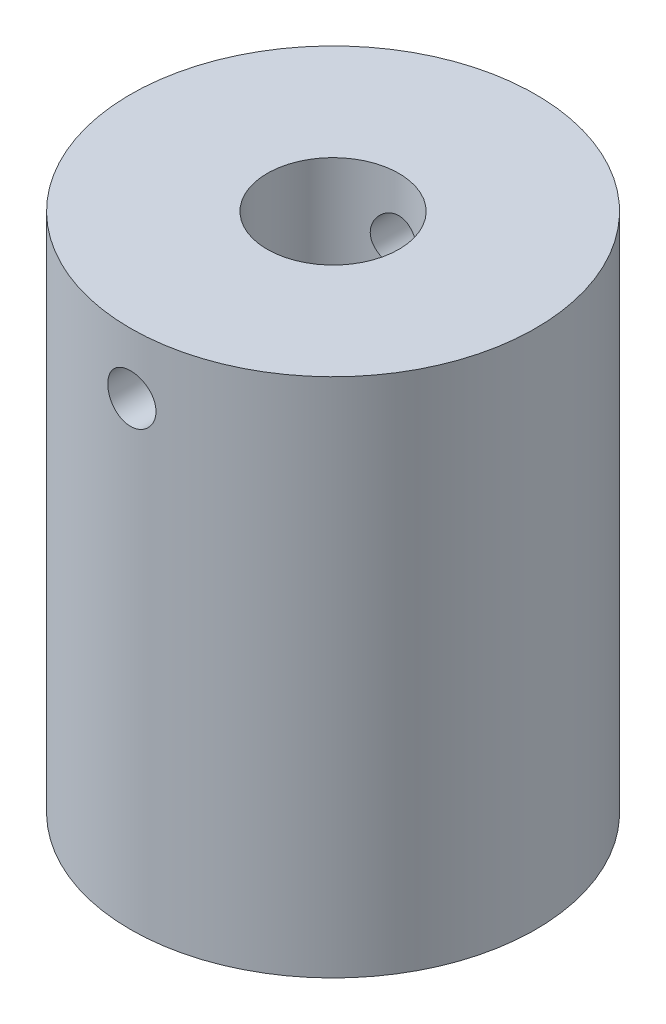
SolidWorks part; units mm, degrees
ref_plane "Front Plane" through (0, 0, 0) normal (0, 0, 1) x (1, 0, 0)
ref_plane "Top Plane" through (0, 0, 0) normal (0, 1, 0) x (1, 0, 0)
ref_plane "Right Plane" through (0, 0, 0) normal (1, 0, 0) x (0, 0, -1)
sketch "Sketch1" plane through (0, 0, 0) normal (0, 1, 0) x (1, 0, 0)
  circle A0 centre (0, 0) radius 7.2571
  dimension "D1" = 14.5143
extrude "Boss-Extrude1" add sketch "Sketch1" along normal blind 18.6509
sketch "Sketch2" plane through (0, 18.6509, 0) normal (0, 1, 0) x (1, 0, 0)
  circle A2 centre (0, 0) radius 2.3586
  dimension "D1" = 4.7171
extrude "Cut-Extrude1" cut sketch "Sketch2" against normal blind 5.4429
sketch "Sketch3" plane through (0, 0, 0) normal (0, -1, 0) x (1, 0, 0)
  line L0 (-1.0089, 1.9812) -> (1.0089, 1.9812)
  arc A0 (-1.4694, 1.8333) -> (1.4694, 1.8333) centre (0, 0) ccw
  arc A1 (-1.0089, 1.9812) -> (-1.4694, 1.8333) centre (-1.2629, 1.9812) ccw
  arc A2 (1.0089, 1.9812) -> (1.4694, 1.8333) centre (1.2629, 1.9812) cw
  dimension "D1" = 4.699
  dimension "D3" = 0.254
  dimension "D2" = 1.9812
extrude "Cut-Extrude2" cut sketch "Sketch3" against normal blind 10.16
ref_plane "Plane1" through (0, 10.16, 0) normal (0, -1, 0) x (-1, 0, 0)
ref_plane "Plane2" through (0, 0, 7.2571) normal (0, 0, 1) x (1, 0, 0)
sketch "Sketch4" plane through (0, 0, 7.2571) normal (0, 0, 1) x (1, 0, 0)
  line L0 (7.2571, 18.6509) -> (-7.2571, 18.6509) construction
  circle A0 centre (0, 16.4737) radius 0.8636
  dimension "D2" = 1.7272
  dimension "D1" = 2.1771
extrude "Cut-Extrude3" cut sketch "Sketch4" against normal through all
scale "Scale1" scale about centroid uniform scaling yes scale factor 1.75
